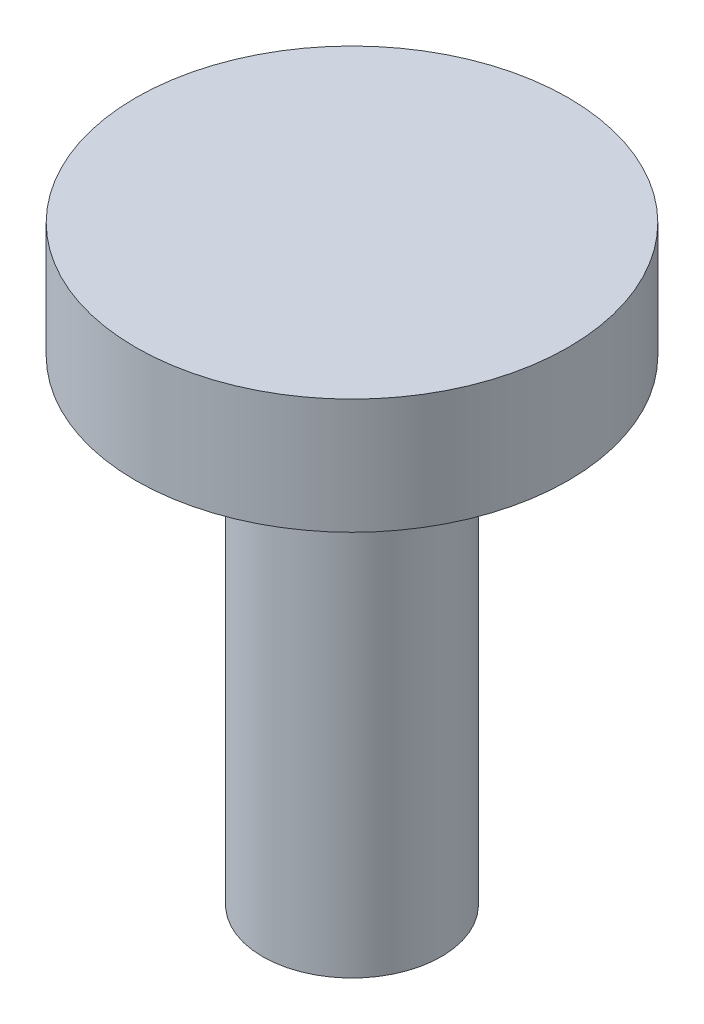
SolidWorks part; units mm, degrees
ref_plane "Спереди" through (0, 0, 0) normal (0, 0, 1) x (1, 0, 0)
ref_plane "Сверху" through (0, 0, 0) normal (0, 1, 0) x (1, 0, 0)
ref_plane "Справа" through (0, 0, 0) normal (1, 0, 0) x (0, 0, -1)
other "Configuration Table"
sketch "Эскиз1" plane through (0, 0, 0) normal (0, 1, 0) x (1, 0, 0)
  circle A0 centre (0, 0) radius 3.1
  dimension "D1" = 6.2
extrude "Бобышка-Вытянуть1" add sketch "Эскиз1" along normal blind 16.5 contours A0
sketch "Эскиз2" plane through (0, 16.5, 0) normal (0, 1, 0) x (1, 0, 0)
  circle A0 centre (0, 0) radius 7.5
  dimension "D1" = 15
extrude "Бобышка-Вытянуть2" add sketch "Эскиз2" along normal blind 4 contours A0
